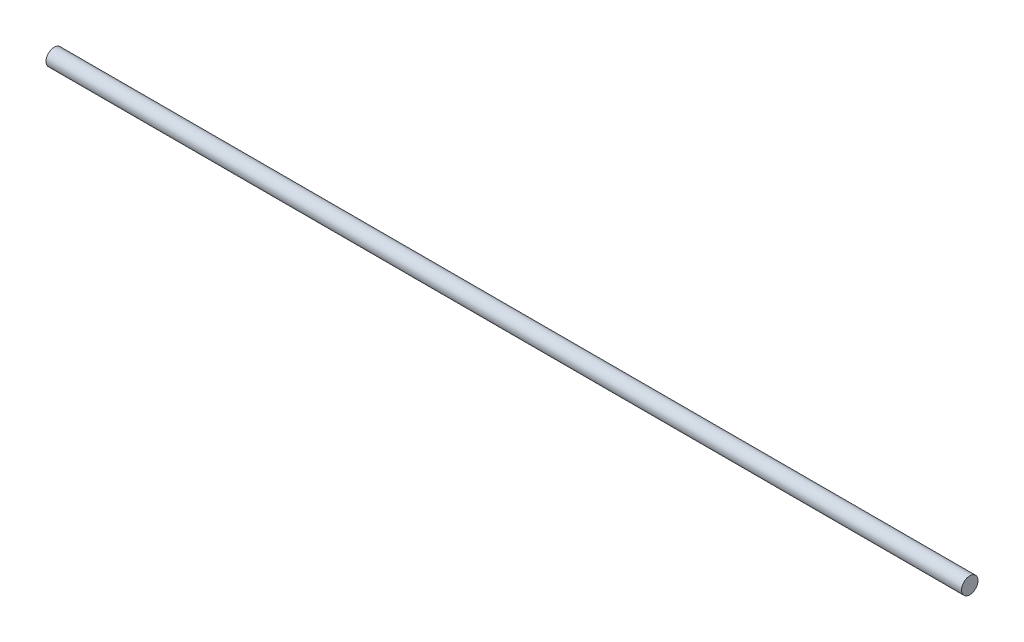
SolidWorks part; units mm, degrees
ref_plane "Front Plane" through (0, 0, 0) normal (0, 0, 1) x (1, 0, 0)
ref_plane "Top Plane" through (0, 0, 0) normal (0, 1, 0) x (1, 0, 0)
ref_plane "Right Plane" through (0, 0, 0) normal (1, 0, 0) x (0, 0, -1)
sketch "Sketch1" plane through (0, 0, 0) normal (0, 0, 1) x (1, 0, 0)
  line L0 (0, 0) -> (167, 0)
  line L1 (0, 0) -> (167, 0) construction
  line L2 (0, 0) -> (0, -1.5)
  line L3 (0, -1.5) -> (167, -1.5)
  line L4 (167, 0) -> (167, -1.5)
  dimension "D1" = 1.5
  dimension "D2" = 167
revolve "Revolve1" add sketch "Sketch1" angle 360 about L1
